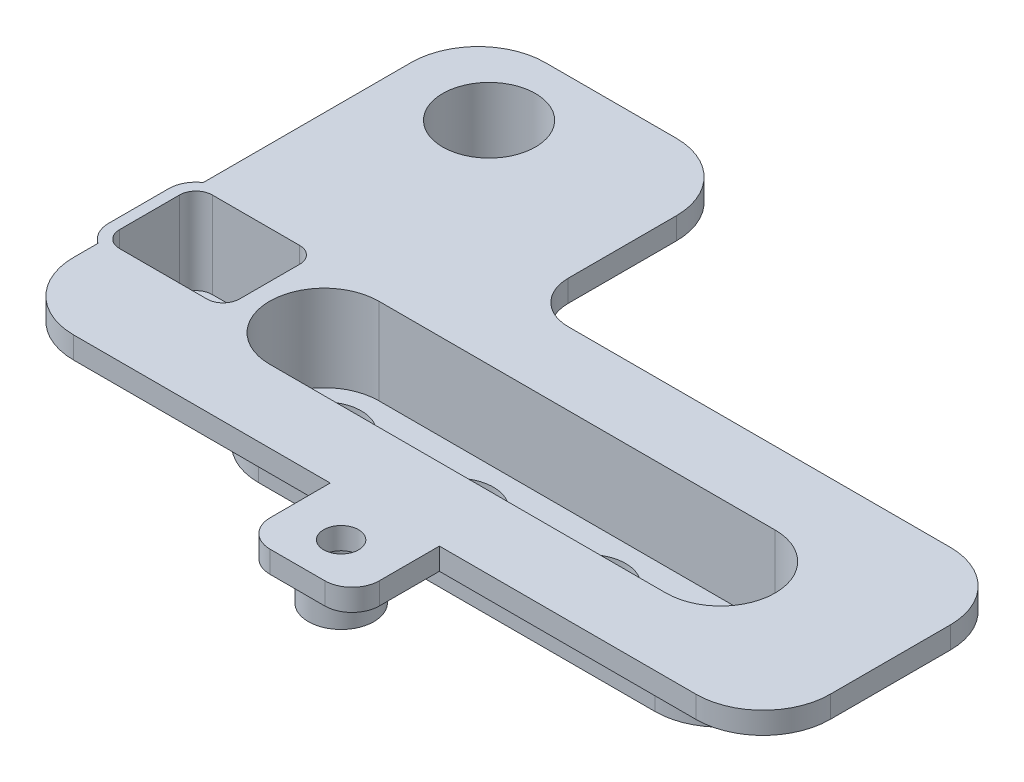
SolidWorks part; units mm, degrees
ref_plane "Спереди" through (0, 0, 0) normal (0, 0, 1) x (1, 0, 0)
ref_plane "Сверху" through (0, 0, 0) normal (0, 1, 0) x (1, 0, 0)
ref_plane "Справа" through (0, 0, 0) normal (1, 0, 0) x (0, 0, -1)
sketch "Эскиз1" plane through (0, 0, 0) normal (0, 1, 0) x (1, 0, 0)
  line L0 (-22, 16.4) -> (-10, 16.4) construction
  line L1 (-3.5, 9.9) -> (-3.5, 0) construction
  line L2 (0, -3.5) -> (35, -3.5) construction
  line L3 (41.5, -10) -> (41.5, -21) construction
  line L4 (35, -27.5) -> (-22, -27.5) construction
  line L5 (-28.5, -21) -> (-28.5, 9.9) construction
  line L6 (35, -27.15) -> (-22, -27.15)
  line L7 (-28.15, -21) -> (-28.15, 9.9)
  line L8 (-22, 16.05) -> (-10, 16.05)
  line L9 (-3.85, 9.9) -> (-3.85, 0)
  line L10 (0, -3.85) -> (35, -3.85)
  line L11 (41.15, -10) -> (41.15, -21)
  arc A0 (-22, 16.4) -> (-28.5, 9.9) centre (-22, 9.9) ccw construction
  arc A1 (-3.5, 9.9) -> (-10, 16.4) centre (-10, 9.9) ccw construction
  arc A2 (-3.5, 0) -> (0, -3.5) centre (0, 0) ccw construction
  arc A3 (41.5, -10) -> (35, -3.5) centre (35, -10) ccw construction
  arc A4 (35, -27.5) -> (41.5, -21) centre (35, -21) ccw construction
  arc A5 (-28.5, -21) -> (-22, -27.5) centre (-22, -21) ccw construction
  arc A6 (-28.15, -21) -> (-22, -27.15) centre (-22, -21) ccw
  arc A7 (-22, 16.05) -> (-28.15, 9.9) centre (-22, 9.9) ccw
  arc A8 (-3.85, 9.9) -> (-10, 16.05) centre (-10, 9.9) ccw
  arc A9 (-3.85, 0) -> (0, -3.85) centre (0, 0) ccw
  arc A10 (41.15, -10) -> (35, -3.85) centre (35, -10) ccw
  arc A11 (35, -27.15) -> (41.15, -21) centre (35, -21) ccw
  dimension "D4" = 6.5
  dimension "D5" = 22
  dimension "D1" = 24
  dimension "D2" = 25
  dimension "D3" = 70
  dimension "D6" = 21
  dimension "D7" = 27.5
  dimension "D8" = 41.5
  dimension "D9" = 16.4
  dimension "D10" = 9.9
  dimension "D11" = 10
  dimension "D12" = 12
  dimension "D13" = 9.9
  dimension "D14" = 11
  dimension "D15" = 35
  dimension "D16" = 0.35
extrude "Бобышка-Вытянуть1" add sketch "Эскиз1" along normal blind 2
sketch "Эскиз2" plane through (0, 2, 0) normal (0, 1, 0) x (1, 0, 0)
  line L0 (-10.7, -21.5) -> (25.6, -21.5)
  line L1 (-10.7, -9.5) -> (25.6, -9.5)
  circle A0 centre (-10.7, -15.5) radius 5 construction
  circle A1 centre (1.4, -15.5) radius 5 construction
  circle A2 centre (13.5, -15.5) radius 5 construction
  circle A3 centre (25.6, -15.5) radius 5 construction
  arc A4 (-10.7, -9.5) -> (-10.7, -21.5) centre (-10.7, -15.5) ccw
  circle A5 centre (1.4, -15.5) radius 6 construction
  circle A6 centre (13.5, -15.5) radius 6 construction
  arc A7 (25.6, -21.5) -> (25.6, -9.5) centre (25.6, -15.5) ccw
  point P13 (-0.2, -15.5)
  point P16 (36.1, -15.5)
  dimension "D1" = 10
  dimension "D2" = 6
  dimension "D3" = 1
  dimension "D4" = 1
  dimension "D5" = 6
extrude "Бобышка-Вытянуть2" add sketch "Эскиз2" against normal offset from surface (8.9 mm away) 0.4
sketch "Эскиз3" plane through (0, 2, 0) normal (0, 1, 0) x (1, 0, 0)
  line L0 (-22.75, -15.9) -> (-22.75, -12) construction
  line L4 (-26.6, -13.95) -> (-18.9, -13.95) construction
  line L6 (-26.75, -18.2) -> (-18.75, -18.2) construction
  line L7 (-28.25, -16.7) -> (-28.25, -11.2) construction
  line L8 (-26.75, -9.7) -> (-18.75, -9.7) construction
  line L9 (-17.25, -16.7) -> (-17.25, -11.2) construction
  line L10 (-28.25, -18.2) -> (-17.25, -9.7) construction
  line L11 (-19.415, -13.0291) -> (-19.415, -12.3)
  line L12 (-19.715, -12) -> (-25.785, -12)
  line L13 (-26.085, -12.3) -> (-26.085, -13.0291)
  line L14 (-26.1574, -13.2245) -> (-26.5276, -13.6559)
  line L15 (-26.6, -13.8513) -> (-26.6, -15.6)
  line L16 (-26.3, -15.9) -> (-19.2, -15.9)
  line L17 (-18.9, -15.6) -> (-18.9, -13.8513)
  line L18 (-18.9724, -13.6559) -> (-19.3426, -13.2245)
  line L19 (-19.415, -13.0291) -> (-19.415, -12.3) construction
  line L20 (-19.715, -12) -> (-25.785, -12) construction
  line L21 (-26.085, -12.3) -> (-26.085, -13.0291) construction
  line L22 (-26.1574, -13.2245) -> (-26.5276, -13.6559) construction
  line L23 (-26.6, -13.8513) -> (-26.6, -15.6) construction
  line L24 (-26.3, -15.9) -> (-19.2, -15.9) construction
  line L25 (-18.9, -15.6) -> (-18.9, -13.8513) construction
  line L26 (-18.9724, -13.6559) -> (-19.3426, -13.2245) construction
  line L27 (-28.25, -9.7) -> (-17.25, -18.2) construction
  line L35 (-26.75, -19.2) -> (-18.75, -19.2)
  line L36 (-16.25, -16.7) -> (-16.25, -11.2)
  line L37 (-26.75, -8.7) -> (-18.75, -8.7)
  line L38 (-29.25, -16.7) -> (-29.25, -11.2)
  arc A0 (-18.75, -18.2) -> (-17.25, -16.7) centre (-18.75, -16.7) ccw construction
  arc A1 (-17.25, -11.2) -> (-18.75, -9.7) centre (-18.75, -11.2) ccw construction
  arc A2 (-26.75, -9.7) -> (-28.25, -11.2) centre (-26.75, -11.2) ccw construction
  arc A3 (-28.25, -16.7) -> (-26.75, -18.2) centre (-26.75, -16.7) ccw construction
  arc A8 (-19.415, -12.3) -> (-19.715, -12) centre (-19.715, -12.3) ccw
  arc A9 (-25.785, -12) -> (-26.085, -12.3) centre (-25.785, -12.3) ccw
  arc A10 (-26.1574, -13.2245) -> (-26.085, -13.0291) centre (-26.385, -13.0291) ccw
  arc A11 (-26.5276, -13.6559) -> (-26.6, -13.8513) centre (-26.3, -13.8513) ccw
  arc A12 (-26.6, -15.6) -> (-26.3, -15.9) centre (-26.3, -15.6) ccw
  arc A13 (-19.2, -15.9) -> (-18.9, -15.6) centre (-19.2, -15.6) ccw
  arc A14 (-18.9, -13.8513) -> (-18.9724, -13.6559) centre (-19.2, -13.8513) ccw
  arc A15 (-19.415, -13.0291) -> (-19.3426, -13.2245) centre (-19.115, -13.0291) ccw
  arc A16 (-19.415, -12.3) -> (-19.715, -12) centre (-19.715, -12.3) ccw construction
  arc A17 (-25.785, -12) -> (-26.085, -12.3) centre (-25.785, -12.3) ccw construction
  arc A18 (-26.1574, -13.2245) -> (-26.085, -13.0291) centre (-26.385, -13.0291) ccw construction
  arc A19 (-26.5276, -13.6559) -> (-26.6, -13.8513) centre (-26.3, -13.8513) ccw construction
  arc A20 (-26.6, -15.6) -> (-26.3, -15.9) centre (-26.3, -15.6) ccw construction
  arc A21 (-19.2, -15.9) -> (-18.9, -15.6) centre (-19.2, -15.6) ccw construction
  arc A22 (-18.9, -13.8513) -> (-18.9724, -13.6559) centre (-19.2, -13.8513) ccw construction
  arc A23 (-19.415, -13.0291) -> (-19.3426, -13.2245) centre (-19.115, -13.0291) ccw construction
  arc A28 (-18.75, -19.2) -> (-16.25, -16.7) centre (-18.75, -16.7) ccw
  arc A29 (-16.25, -11.2) -> (-18.75, -8.7) centre (-18.75, -11.2) ccw
  arc A30 (-26.75, -8.7) -> (-29.25, -11.2) centre (-26.75, -11.2) ccw
  arc A31 (-29.25, -16.7) -> (-26.75, -19.2) centre (-26.75, -16.7) ccw
  point P4 (-22.75, -13.95)
  point P5 (-22.75, -13.95)
  dimension "D4" = 1.5
  dimension "D2" = 11
  dimension "D3" = 8.5
  dimension "D1" = 0
  dimension "D5" = 1
extrude "Бобышка-Вытянуть3" add sketch "Эскиз3" against normal offset from surface (8.9 mm away) 0.4
sketch "Эскиз5" plane through (0, 2, 0) normal (0, 1, 0) x (1, 0, 0)
  line L4 (25.6, -10.5) -> (-10.7, -10.5)
  line L5 (-10.7, -20.5) -> (25.6, -20.5)
  line L18 (25.6, -10.5) -> (-10.7, -10.5)
  line L19 (-10.7, -20.5) -> (25.6, -20.5)
  arc A4 (25.6, -20.5) -> (25.6, -10.5) centre (25.6, -15.5) ccw
  arc A5 (-10.7, -10.5) -> (-10.7, -20.5) centre (-10.7, -15.5) ccw
  arc A18 (25.6, -20.5) -> (25.6, -10.5) centre (25.6, -15.5) ccw
  arc A19 (-10.7, -10.5) -> (-10.7, -20.5) centre (-10.7, -15.5) ccw
  dimension "D2" = 1
extrude "Вырез-Вытянуть1" cut sketch "Эскиз5" against normal offset from surface (7.9 mm away) 1 up to face at (-12.6165, -6.9, 14.4243)
sketch "Эскиз6" plane through (0, 2, 0) normal (0, 1, 0) x (1, 0, 0)
  line L0 (-17.25, -16.7) -> (-17.25, -11.2) construction
  line L1 (-26.75, -18.2) -> (-18.75, -18.2) construction
  line L2 (-28.25, -16.7) -> (-28.25, -11.2) construction
  line L3 (-26.75, -9.7) -> (-18.75, -9.7) construction
  line L4 (-17.25, -16.7) -> (-17.25, -11.2)
  line L5 (-26.75, -18.2) -> (-18.75, -18.2)
  line L6 (-28.25, -16.7) -> (-28.25, -11.2)
  line L7 (-26.75, -9.7) -> (-18.75, -9.7)
  arc A0 (-17.25, -11.2) -> (-18.75, -9.7) centre (-18.75, -11.2) ccw construction
  arc A1 (-18.75, -18.2) -> (-17.25, -16.7) centre (-18.75, -16.7) ccw construction
  arc A2 (-28.25, -16.7) -> (-26.75, -18.2) centre (-26.75, -16.7) ccw construction
  arc A3 (-26.75, -9.7) -> (-28.25, -11.2) centre (-26.75, -11.2) ccw construction
  arc A4 (-17.25, -11.2) -> (-18.75, -9.7) centre (-18.75, -11.2) ccw
  arc A5 (-18.75, -18.2) -> (-17.25, -16.7) centre (-18.75, -16.7) ccw
  arc A6 (-28.25, -16.7) -> (-26.75, -18.2) centre (-26.75, -16.7) ccw
  arc A7 (-26.75, -9.7) -> (-28.25, -11.2) centre (-26.75, -11.2) ccw
extrude "Вырез-Вытянуть2" cut sketch "Эскиз6" against normal offset from surface (7.9 mm away) 1 up to face at (-12.6165, -6.9, 14.4243)
sketch "Эскиз7" plane through (0, 2, 0) normal (0, 1, 0) x (1, 0, 0)
  circle A0 centre (-20, 8.9) radius 3.2 construction
  circle A1 centre (-20, 8.9) radius 3.2 construction
  circle A2 centre (-20, 8.9) radius 4.75
  dimension "D1" = 9.5
extrude "Бобышка-Вытянуть4" add sketch "Эскиз7" against normal offset from surface (8.9 mm away) 0.4
sketch "Эскиз8" plane through (0, 2, 0) normal (0, 1, 0) x (1, 0, 0)
  circle A0 centre (-20, 8.9) radius 4.25
  dimension "D1" = 8.5
extrude "Вырез-Вытянуть3" cut sketch "Эскиз8" against normal offset from surface (7.9 mm away) 1 up to face at (-15.25, -6.9, -8.9)
sketch "Эскиз9" plane through (0, -5.9, 0) normal (0, 1, 0) x (1, 0, 0)
  circle A0 centre (-10.7, -15.5) radius 3.4
  circle A1 centre (1.4, -15.5) radius 3.4
  circle A2 centre (13.5, -15.5) radius 3.4
  circle A3 centre (25.6, -15.5) radius 3.4
  circle A4 centre (-10.7, -15.5) radius 3 construction
  dimension "D1" = 0.4
extrude "Вырез-Вытянуть4" cut sketch "Эскиз9" against normal through all
sketch "Эскиз10" plane through (0, -5.9, 0) normal (0, 1, 0) x (1, 0, 0)
  circle A0 centre (-20, 8.9) radius 3.55
  circle A1 centre (-20, 8.9) radius 3.2 construction
  dimension "D1" = 0.35
extrude "Вырез-Вытянуть5" cut sketch "Эскиз10" against normal through all
sketch "Эскиз11" plane through (0, -5.9, 0) normal (0, 1, 0) x (1, 0, 0)
  line L0 (-26.6, -13.8513) -> (-26.6, -15.6) construction
  line L1 (-26.3, -15.9) -> (-19.2, -15.9) construction
  line L2 (-18.9, -15.6) -> (-18.9, -13.8513) construction
  line L3 (-18.9724, -13.6559) -> (-19.3426, -13.2245) construction
  line L4 (-19.415, -13.0291) -> (-19.415, -12.3) construction
  line L5 (-19.715, -12) -> (-25.785, -12) construction
  line L6 (-26.085, -12.3) -> (-26.085, -13.0291) construction
  line L7 (-26.1574, -13.2245) -> (-26.5276, -13.6559) construction
  line L8 (-26.6, -13.8513) -> (-26.6, -15.6) construction
  line L9 (-26.3, -15.9) -> (-19.2, -15.9) construction
  line L10 (-18.9, -15.6) -> (-18.9, -13.8513) construction
  line L11 (-18.9724, -13.6559) -> (-19.3426, -13.2245) construction
  line L12 (-19.415, -13.0291) -> (-19.415, -12.3) construction
  line L13 (-19.715, -12) -> (-25.785, -12) construction
  line L14 (-26.085, -12.3) -> (-26.085, -13.0291) construction
  line L15 (-26.1574, -13.2245) -> (-26.5276, -13.6559) construction
  line L16 (-27, -13.8513) -> (-27, -15.6)
  line L17 (-26.3, -16.3) -> (-19.2, -16.3)
  line L18 (-18.5, -15.6) -> (-18.5, -13.8513)
  line L19 (-18.6688, -13.3953) -> (-19.015, -12.992)
  line L20 (-19.015, -12.992) -> (-19.015, -12.3)
  line L21 (-19.715, -11.6) -> (-25.785, -11.6)
  line L22 (-26.485, -12.3) -> (-26.485, -12.992)
  line L23 (-26.485, -12.992) -> (-26.8312, -13.3953)
  arc A0 (-26.5276, -13.6559) -> (-26.6, -13.8513) centre (-26.3, -13.8513) ccw construction
  arc A1 (-26.6, -15.6) -> (-26.3, -15.9) centre (-26.3, -15.6) ccw construction
  arc A2 (-19.2, -15.9) -> (-18.9, -15.6) centre (-19.2, -15.6) ccw construction
  arc A3 (-18.9, -13.8513) -> (-18.9724, -13.6559) centre (-19.2, -13.8513) ccw construction
  arc A4 (-19.415, -13.0291) -> (-19.3426, -13.2245) centre (-19.115, -13.0291) ccw construction
  arc A5 (-19.415, -12.3) -> (-19.715, -12) centre (-19.715, -12.3) ccw construction
  arc A6 (-25.785, -12) -> (-26.085, -12.3) centre (-25.785, -12.3) ccw construction
  arc A7 (-26.1574, -13.2245) -> (-26.085, -13.0291) centre (-26.385, -13.0291) ccw construction
  arc A8 (-26.5276, -13.6559) -> (-26.6, -13.8513) centre (-26.3, -13.8513) ccw construction
  arc A9 (-26.6, -15.6) -> (-26.3, -15.9) centre (-26.3, -15.6) ccw construction
  arc A10 (-19.2, -15.9) -> (-18.9, -15.6) centre (-19.2, -15.6) ccw construction
  arc A11 (-18.9, -13.8513) -> (-18.9724, -13.6559) centre (-19.2, -13.8513) ccw construction
  arc A12 (-19.415, -13.0291) -> (-19.3426, -13.2245) centre (-19.115, -13.0291) ccw construction
  arc A13 (-19.415, -12.3) -> (-19.715, -12) centre (-19.715, -12.3) ccw construction
  arc A14 (-25.785, -12) -> (-26.085, -12.3) centre (-25.785, -12.3) ccw construction
  arc A15 (-26.1574, -13.2245) -> (-26.085, -13.0291) centre (-26.385, -13.0291) ccw construction
  arc A16 (-27, -15.6) -> (-26.3, -16.3) centre (-26.3, -15.6) ccw
  arc A17 (-19.2, -16.3) -> (-18.5, -15.6) centre (-19.2, -15.6) ccw
  arc A18 (-18.5, -13.8513) -> (-18.6688, -13.3953) centre (-19.2, -13.8513) ccw
  arc A19 (-19.015, -12.992) -> (-19.015, -12.992) centre (-19.015, -12.992) ccw
  arc A20 (-19.015, -12.3) -> (-19.715, -11.6) centre (-19.715, -12.3) ccw
  arc A21 (-25.785, -11.6) -> (-26.485, -12.3) centre (-25.785, -12.3) ccw
  arc A22 (-26.485, -12.992) -> (-26.485, -12.992) centre (-26.485, -12.992) ccw
  arc A23 (-26.8312, -13.3953) -> (-27, -13.8513) centre (-26.3, -13.8513) ccw
  dimension "D1" = 0.4
extrude "Вырез-Вытянуть6" cut sketch "Эскиз11" against normal through all
sketch "Эскиз12" plane through (0, 0, 0) normal (0, -1, 0) x (1, 0, 0)
  line L0 (6.5, 27.15) -> (6.5, 3.85) construction
  line L1 (-22, 27.15) -> (35, 27.15) construction
  line L2 (35, 3.85) -> (0, 3.85) construction
  line L3 (6.5, 27.15) -> (6.5, 35.15) construction
  line L4 (1.5, 27.15) -> (11.5, 27.15)
  line L5 (1.5, 27.15) -> (1.5, 32.65)
  line L6 (4, 35.15) -> (9, 35.15)
  line L7 (11.5, 27.15) -> (11.5, 32.65)
  arc A0 (9, 35.15) -> (11.5, 32.65) centre (9, 32.65) cw
  arc A1 (4, 35.15) -> (1.5, 32.65) centre (4, 32.65) ccw
  point P12 (11.5, 35.15)
  point P15 (1.5, 35.15)
  dimension "D3" = 2.5
  dimension "D1" = 10
  dimension "D2" = 8
extrude "Бобышка-Вытянуть5" add sketch "Эскиз12" against normal up to surface (2 mm away) up to face at (-20, 2, -4.65)
sketch "Эскиз13" plane through (0, 0, 0) normal (0, -1, 0) x (1, 0, 0)
  line L0 (6.5, 27.15) -> (6.5, 35.15) construction
  circle A0 centre (6.5, 31.15) radius 3
  dimension "D1" = 6
extrude "Бобышка-Вытянуть6" add sketch "Эскиз13" along normal blind 3
sketch "Эскиз14" plane through (0, -3, 0) normal (0, -1, 0) x (1, 0, 0)
  circle A0 centre (6.5, 31.15) radius 1.6
  dimension "D1" = 3.2
extrude "Вырез-Вытянуть7" cut sketch "Эскиз14" against normal through all
sketch "Эскиз15" plane through (0, -3, 0) normal (0, -1, 0) x (1, 0, 0)
  circle A0 centre (6.5, 31.15) radius 1.75
  dimension "D1" = 3.5
extrude "Вырез-Вытянуть8" cut sketch "Эскиз15" against normal blind 3
